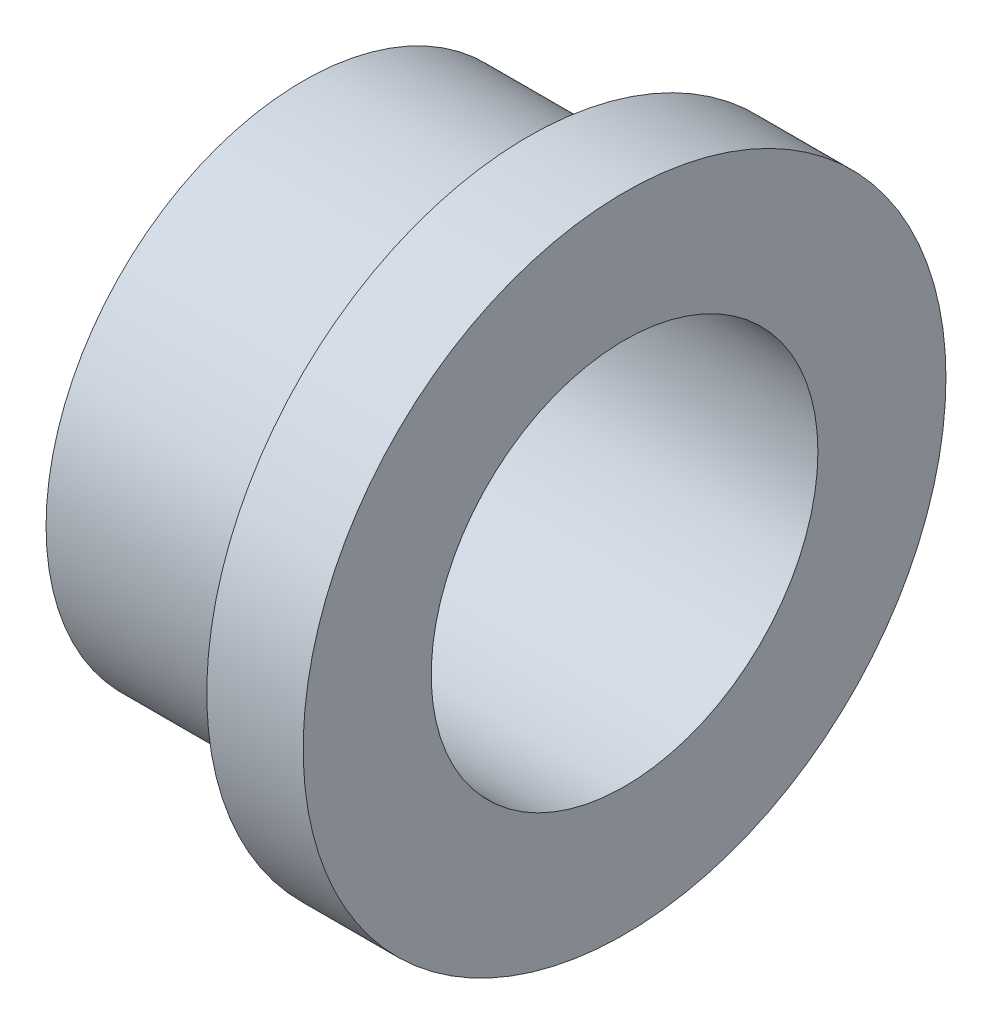
SolidWorks part; units mm, degrees
material "Tin Bearing Bronze"
ref_plane "Front Plane" through (0, 0, 0) normal (0, 0, 1) x (1, 0, 0)
ref_plane "Top Plane" through (0, 0, 0) normal (0, 1, 0) x (1, 0, 0)
ref_plane "Right Plane" through (0, 0, 0) normal (1, 0, 0) x (0, 0, -1)
sketch "Sketch1" plane through (0, 0, 0) normal (1, 0, 0) x (0, 0, -1)
  circle A0 centre (0, 0) radius 9.5504
  circle A1 centre (0, 0) radius 12.7
extrude "Boss-Extrude1" add sketch "Sketch1" against normal blind 15.875
sketch "Sketch3" plane through (0, 0, 0) normal (1, 0, 0) x (0, 0, -1)
  circle A0 centre (0, 0) radius 15.875
  circle A1 centre (0, 0) radius 9.5504
  dimension "D1" = 31.75
extrude "Boss-Extrude2" add sketch "Sketch3" against normal blind 4.7625
